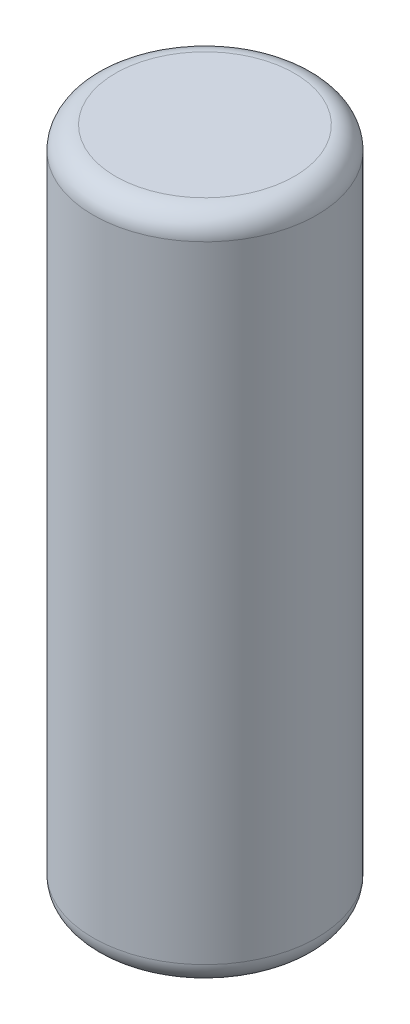
SolidWorks part; units mm, degrees
material "Silicon"
ref_plane "Front Plane" through (0, 0, 0) normal (0, 0, 1) x (1, 0, 0)
ref_plane "Top Plane" through (0, 0, 0) normal (0, 1, 0) x (1, 0, 0)
ref_plane "Right Plane" through (0, 0, 0) normal (1, 0, 0) x (0, 0, -1)
sketch "Main Parachute Bag Profile" plane through (0, 0, 0) normal (0, 1, 0) x (1, 0, 0)
  circle A0 centre (0, 0) radius 63.5
  dimension "D1" = 127
extrude "Main Parachute Bag Body" add sketch "Main Parachute Bag Profile" along normal blind 381 contours A0
fillet "Fillet1" radius 12.7 2 edges at (0, 0, 63.5) (0, 381, 63.5)
equation "\"Packed Length\"= 15"
equation "\"Packed Diameter\"= 5"
equation "\"D1@Main Parachute Bag Body\"=\"Packed Length\""
equation "\"D1@Main Parachute Bag Profile\"=\"Packed Diameter\""
